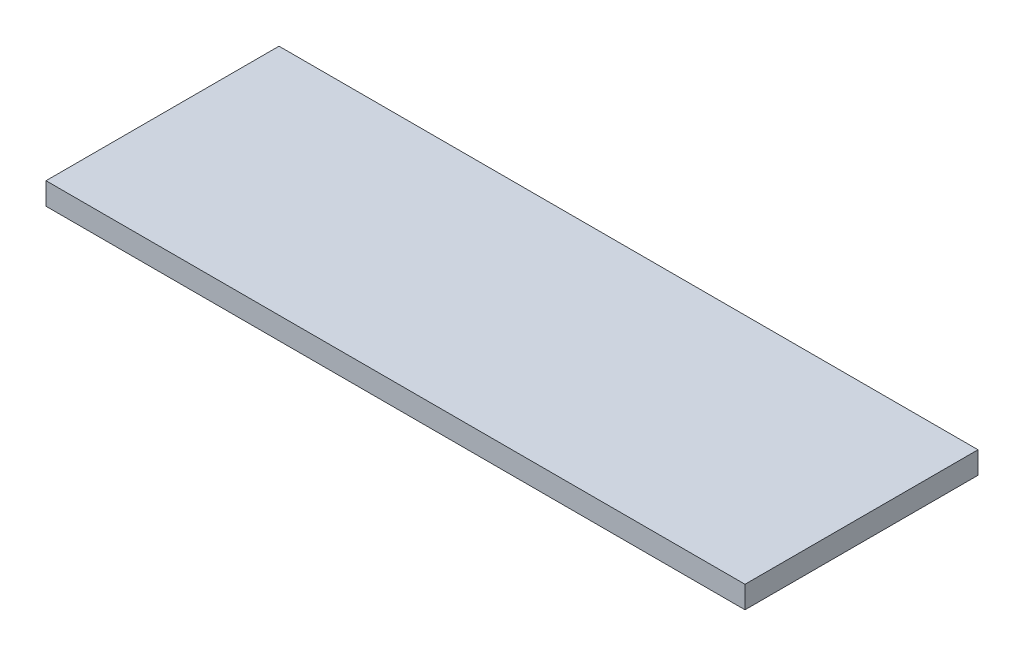
SolidWorks part; units mm, degrees
material "Silicon"
ref_plane "Front Plane" through (0, 0, 0) normal (0, 0, 1) x (1, 0, 0)
ref_plane "Top Plane" through (0, 0, 0) normal (0, 1, 0) x (1, 0, 0)
ref_plane "Right Plane" through (0, 0, 0) normal (1, 0, 0) x (0, 0, -1)
sketch "Sketch1" plane through (0, 0, 0) normal (0, 1, 0) x (1, 0, 0)
  line L0 (-30, 10) -> (30, 10)
  line L1 (-30, 10) -> (-30, -10)
  line L2 (30, 10) -> (30, -10)
  line L3 (-30, -10) -> (30, -10)
  line L4 (0, 10) -> (0, -10) construction
  dimension "D1" = 60
  dimension "D2" = 20
extrude "Boss-Extrude1" add sketch "Sketch1" along normal blind 1.9
